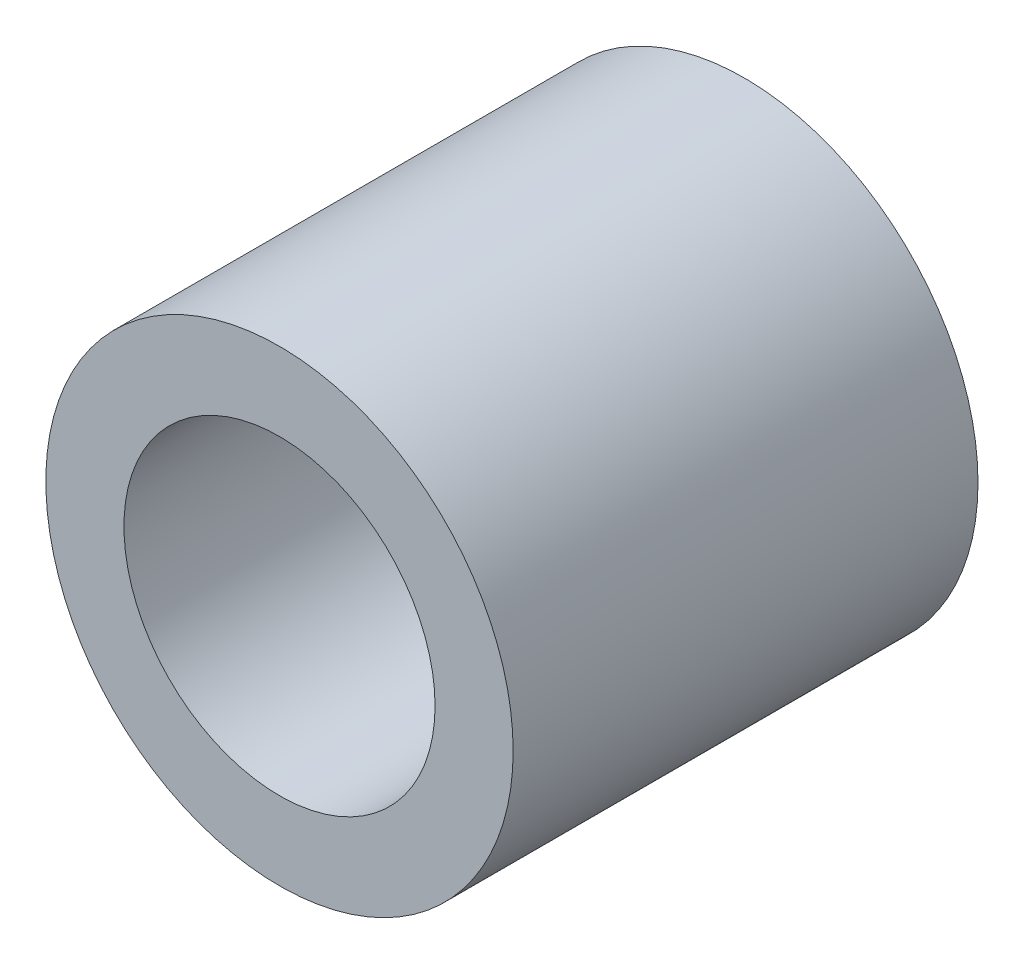
SolidWorks part; units mm, degrees
ref_plane "Front Plane" through (0, 0, 0) normal (0, 0, 1) x (1, 0, 0)
ref_plane "Top Plane" through (0, 0, 0) normal (0, 1, 0) x (1, 0, 0)
ref_plane "Right Plane" through (0, 0, 0) normal (1, 0, 0) x (0, 0, -1)
sketch "Sketch1" plane through (0, 0, 0) normal (0, 0, 1) x (1, 0, 0)
  circle A0 centre (0, 0) radius 4.7879
  circle A1 centre (0, 0) radius 3.1877
  dimension "D1" = 9.5758
  dimension "ID" = 6.3754
extrude "Extrude1" add sketch "Sketch1" along normal mid plane 9.525
sketch "Sketch2" plane through (0, 0, 0) normal (1, 0, 0) x (0, 0, -1)
  line L0 (-4.7625, -3.1877) -> (4.7625, -3.1877) construction
  line L3 (4.7625, 3.1877) -> (-4.7625, 3.1877) construction
  line L5 (-4.7625, -3.1877) -> (4.7625, -3.1877)
  line L6 (4.7625, 3.1877) -> (-4.7625, 3.1877)
sketch "Sketch4" plane through (0, 0, 4.7625) normal (0, 0, 1) x (1, 0, 0)
  line L0 (0, 0) -> (-2.254, 2.254)
  line L1 (0, -10.4775) -> (0, 10.4775) construction
  circle A0 centre (0, 0) radius 3.1877 construction
  dimension "D1" = 45
